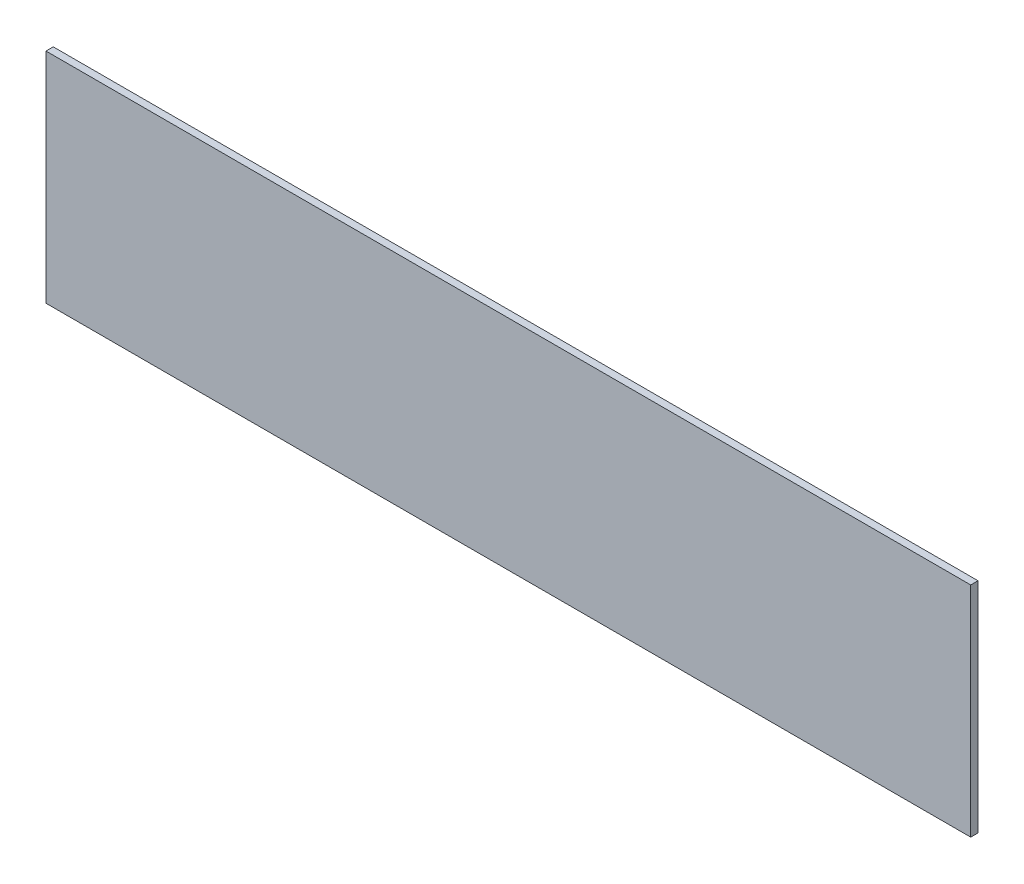
SolidWorks part; units mm, degrees
ref_plane "Front Plane" through (0, 0, 0) normal (0, 0, 1) x (1, 0, 0)
ref_plane "Top Plane" through (0, 0, 0) normal (0, 1, 0) x (1, 0, 0)
ref_plane "Right Plane" through (0, 0, 0) normal (1, 0, 0) x (0, 0, -1)
sketch "Sketch1" plane through (0, 0, 0) normal (0, 0, 1) x (1, 0, 0)
  line L1 (95.25, -22.5) -> (-95.25, -22.5)
  line L2 (95.25, -22.5) -> (95.25, 22.5)
  line L3 (95.25, 22.5) -> (-95.25, 22.5)
  line L4 (-95.25, -22.5) -> (-95.25, 22.5)
  line L5 (95.25, -22.5) -> (-95.25, 22.5) construction
  line L6 (95.25, 22.5) -> (-95.25, -22.5) construction
  point P0 (0, 0)
extrude "Boss-Extrude1" add sketch "Sketch1" along normal blind 1.5
